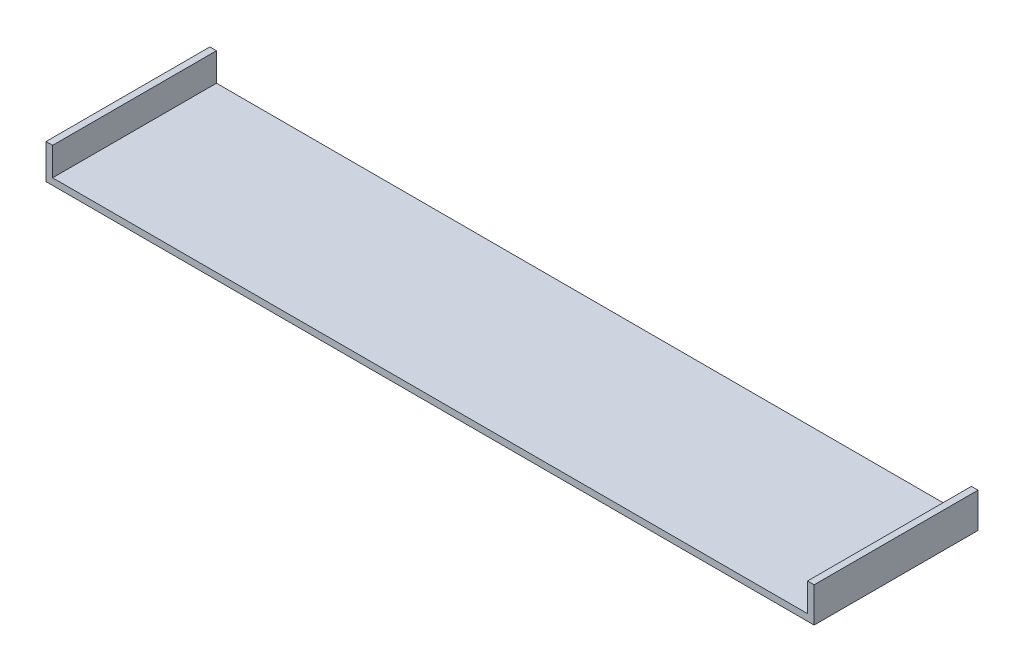
SolidWorks part; units mm, degrees
ref_plane "Front Plane" through (0, 0, 0) normal (0, 0, 1) x (1, 0, 0)
ref_plane "Top Plane" through (0, 0, 0) normal (0, 1, 0) x (1, 0, 0)
ref_plane "Right Plane" through (0, 0, 0) normal (1, 0, 0) x (0, 0, -1)
sketch "Sketch1" plane through (0, 0, 0) normal (0, 0, 1) x (1, 0, 0)
  line L0 (-250.5141, 25.7536) -> (-250.5141, 0)
  line L1 (-250.5141, 0) -> (440.5033, 0)
  line L2 (440.5033, 0) -> (440.5033, 25.9157)
  dimension "D1" = 691.0174
  dimension "D2" = 250.5141
  dimension "D3" = 25.7536
  dimension "D4" = 25.9157
extrude "Extrude-Thin1" add sketch "Sketch1" along normal blind 150 thin
